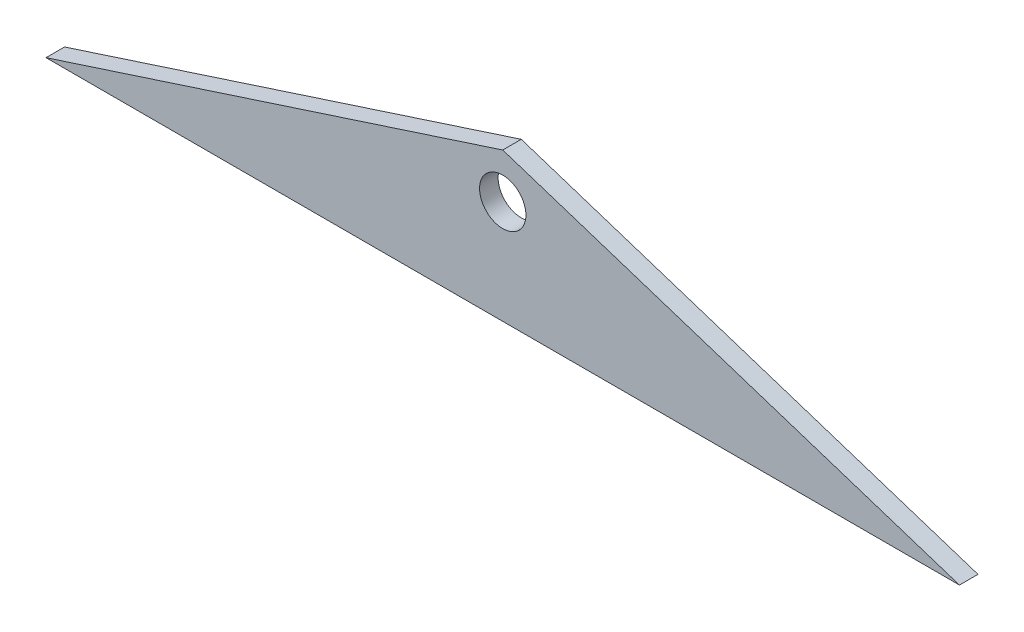
SolidWorks part; units mm, degrees
ref_plane "Front" through (0, 0, 0) normal (0, 0, 1) x (1, 0, 0)
ref_plane "Top" through (0, 0, 0) normal (0, 1, 0) x (1, 0, 0)
ref_plane "Right" through (0, 0, 0) normal (1, 0, 0) x (0, 0, -1)
sketch "Sketch1" plane through (0, 0, 0) normal (0, 0, 1) x (1, 0, 0)
  line L0 (78.1732, -379.6723) -> (0, -354.2723)
  line L1 (0, -354.2723) -> (-78.1732, -379.6723)
  line L2 (-0.3538, -354.3873) -> (-62.9376, -374.722) construction
  line L4 (62.9376, -374.722) -> (0.3538, -354.3873) construction
  line L5 (-78.1732, -379.6723) -> (78.1732, -379.6723)
  line L6 (0, -379.6723) -> (0, -354.2723) construction
  dimension "D1" = 25.4
extrude "Extrude1" add sketch "Sketch1" along normal blind 3.175
sketch "Sketch2" plane through (0, 0, 3.175) normal (0, 0, 1) x (1, 0, 0)
  circle A0 centre (0, -361.95) radius 3.9688
  circle A1 centre (0, -361.95) radius 3.556 construction
  dimension "D1" = 7.9375
extrude "Cut-Extrude1" cut sketch "Sketch2" against normal up to next
